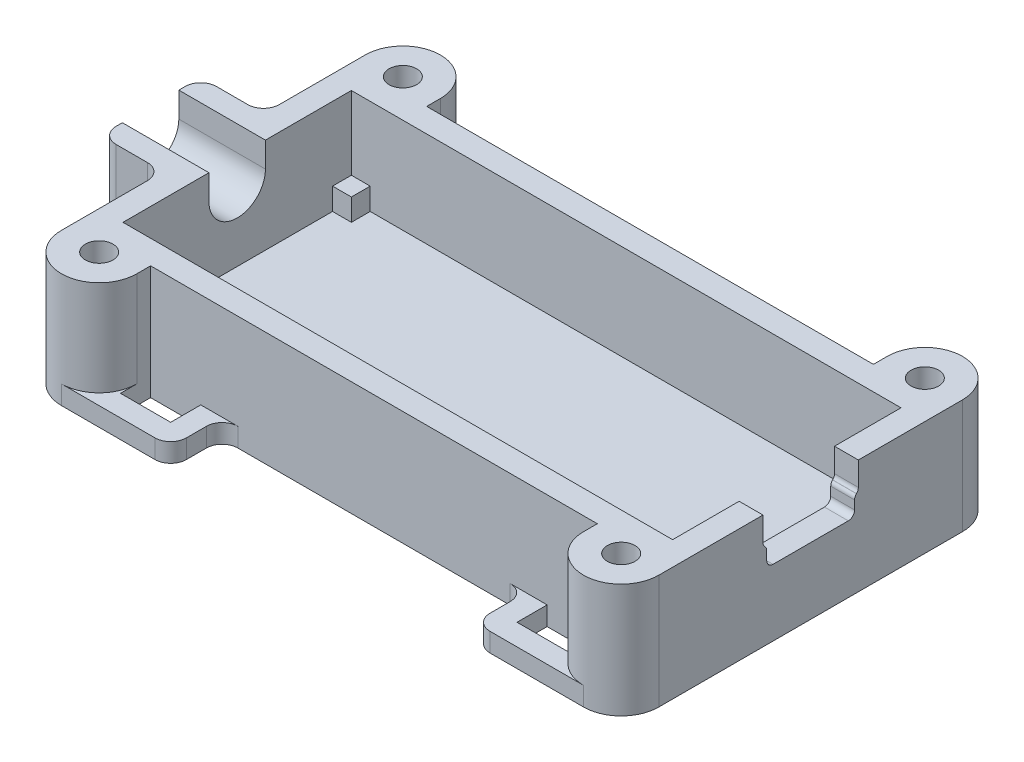
SolidWorks part; units mm, degrees
ref_plane "Front Plane" through (0, 0, 0) normal (0, 0, 1) x (1, 0, 0)
ref_plane "Top Plane" through (0, 0, 0) normal (0, 1, 0) x (1, 0, 0)
ref_plane "Right Plane" through (0, 0, 0) normal (1, 0, 0) x (0, 0, -1)
sketch "Sketch1" plane through (0, 0, 0) normal (0, 1, 0) x (1, 0, 0)
  line L0 (-21.9, 9.1) -> (-23.8, 9.1) construction
  line L1 (-21.9, 9.1) -> (21.9, 9.1)
  line L2 (-21.9, 9.1) -> (-21.9, -9.1)
  line L3 (-21.9, -9.1) -> (21.9, -9.1)
  line L4 (21.9, 9.1) -> (21.9, -9.1)
  line L5 (-21.9, 9.1) -> (21.9, -9.1) construction
  line L6 (-21.9, -9.1) -> (21.9, 9.1) construction
  line L7 (23.8, -11) -> (-23.8, -11)
  line L8 (23.8, -11) -> (23.8, 11)
  line L9 (23.8, 11) -> (-23.8, 11)
  line L10 (-23.8, -11) -> (-23.8, 11)
  line L11 (23.8, -11) -> (-23.8, 11) construction
  line L12 (23.8, 11) -> (-23.8, -11) construction
  line L13 (-21.9, 9.1) -> (-21.9, 11) construction
  line L14 (-19.7, 12.1) -> (-17.8, 12.1) construction
  line L15 (-23.8, 12.1) -> (-23.8, 11)
  line L16 (0, 30.5142) -> (0, -27.0472) construction
  line L17 (-40.1948, 0) -> (31.8876, 0) construction
  line L18 (-17.8, 12.1) -> (-17.8, 11)
  line L19 (17.8, 12.1) -> (17.8, 11)
  line L20 (23.8, 12.1) -> (23.8, 11)
  line L21 (23.8, -12.1) -> (23.8, -11)
  line L22 (17.8, -12.1) -> (17.8, -11)
  line L23 (-17.8, -12.1) -> (-17.8, -11)
  line L24 (-23.8, -12.1) -> (-23.8, -11)
  line L26 (-28.8, 4) -> (-23.8, 4)
  line L27 (-28.8, 4) -> (-28.8, -4)
  line L28 (-28.8, -4) -> (-23.8, -4)
  line L29 (-23.8, 4) -> (-23.8, -4)
  line L30 (-28.8, 4) -> (-23.8, -4) construction
  line L31 (-28.8, -4) -> (-23.8, 4) construction
  circle A0 centre (-20.8, 12.1) radius 1.1
  circle A1 centre (-20.8, 12.1) radius 3
  circle A2 centre (20.8, 12.1) radius 1.1
  circle A3 centre (20.8, 12.1) radius 3
  circle A4 centre (20.8, -12.1) radius 1.1
  circle A5 centre (20.8, -12.1) radius 3
  circle A6 centre (-20.8, -12.1) radius 1.1
  circle A7 centre (-20.8, -12.1) radius 3
  point P0 (0, 0)
  point P6 (0, 0)
  point P42 (-26.3, 0)
  dimension "D4" = 2.2
  dimension "D5" = 5
  dimension "D3" = 6
  dimension "D1" = 18.2
  dimension "D2" = 43.8
  dimension "D6" = 8
extrude "Boss-Extrude1" add sketch "Sketch1" along normal blind 7.6 contours A1 L9 L18 | L9 A1 A0 | A1 L15 L9 | L9 A3 L19 | A3 L9 A2 | L20 A3 L9 | A5 L7 L22 | A5 L7 A4 | A5 L21 L7 | L24 A7 L7 | A7 L7 A6 | L7 A7 L23 | L7 A7 L3 L2 L1 A1 L9 L10 | A7 L7 | L3 A7 L7 A5 | L7 A5 | A5 L7 L8 L9 A3 L1 L4 L3 | A3 L9 | L1 A3 L9 A1 | A1 L9 | L27 L28 L10 L26
sketch "Sketch3" plane through (0, 0, 0) normal (0, -1, 0) x (1, 0, 0)
  line L8 (-23.8, -4) -> (-23.8, -12.1)
  line L9 (-17.8, -12.1) -> (-17.8, -11)
  line L10 (-17.8, -11) -> (17.8, -11)
  line L11 (17.8, -11) -> (17.8, -12.1)
  line L12 (23.8, -12.1) -> (23.8, 12.1)
  line L13 (17.8, 12.1) -> (17.8, 11)
  line L14 (17.8, 11) -> (-17.8, 11)
  line L15 (-17.8, 11) -> (-17.8, 12.1)
  line L16 (-23.8, -4) -> (-23.8, -12.1)
  line L17 (-17.8, -12.1) -> (-17.8, -11)
  line L18 (-17.8, -11) -> (17.8, -11)
  line L19 (17.8, -11) -> (17.8, -12.1)
  line L20 (23.8, -12.1) -> (23.8, 12.1)
  line L21 (17.8, 12.1) -> (17.8, 11)
  line L22 (17.8, 11) -> (-17.8, 11)
  line L23 (-17.8, 11) -> (-17.8, 12.1)
  line L28 (-23.8, 12.1) -> (-23.8, 4)
  line L29 (-23.8, 12.1) -> (-23.8, 4)
  line L30 (-23.8, 4) -> (-28.8, 4)
  line L31 (-23.8, 4) -> (-28.8, 4)
  line L32 (-28.8, 4) -> (-28.8, -4)
  line L33 (-28.8, 4) -> (-28.8, -4)
  line L34 (-28.8, -4) -> (-23.8, -4)
  line L35 (-28.8, -4) -> (-23.8, -4)
  circle A0 centre (-20.8, -12.1) radius 1.1 construction
  circle A1 centre (20.8, -12.1) radius 1.1 construction
  circle A2 centre (20.8, 12.1) radius 1.1 construction
  circle A3 centre (-20.8, 12.1) radius 1.1 construction
  arc A4 (-17.8, 12.1) -> (-23.8, 12.1) centre (-20.8, 12.1) ccw
  arc A5 (-23.8, -12.1) -> (-17.8, -12.1) centre (-20.8, -12.1) ccw
  arc A6 (17.8, -12.1) -> (23.8, -12.1) centre (20.8, -12.1) ccw
  arc A7 (23.8, 12.1) -> (17.8, 12.1) centre (20.8, 12.1) ccw
  arc A8 (-17.8, 12.1) -> (-23.8, 12.1) centre (-20.8, 12.1) ccw
  arc A9 (-23.8, -12.1) -> (-17.8, -12.1) centre (-20.8, -12.1) ccw
  arc A10 (17.8, -12.1) -> (23.8, -12.1) centre (20.8, -12.1) ccw
  arc A11 (23.8, 12.1) -> (17.8, 12.1) centre (20.8, 12.1) ccw
  circle A12 centre (-20.8, -12.1) radius 1.1
  circle A13 centre (20.8, -12.1) radius 1.1
  circle A14 centre (20.8, 12.1) radius 1.1
  circle A15 centre (-20.8, 12.1) radius 1.1
  dimension "D1" = 0
extrude "Boss-Extrude2" add sketch "Sketch3" along normal blind 1.5
sketch "Sketch4" plane through (-28.8, 0, 0) normal (-1, 0, 0) x (0, 0, 1)
  line L0 (-9.1, 0) -> (9.1, 0) construction
  line L1 (-9.1, 0) -> (9.1, 0)
  line L2 (0, 7.6) -> (0, -1.5) construction
  line L3 (-4, 7.6) -> (-12.1, 7.6) construction
  line L5 (0, 3.35) -> (12.1, 3.35) construction
  line L6 (12.1, 7.6) -> (12.1, -1.5) construction
  line L7 (-2.25, 5.6) -> (-2.25, 7.6)
  line L8 (2.25, 5.6) -> (2.25, 7.6)
  line L9 (-2.25, 7.6) -> (2.25, 7.6)
  line L11 (-4, 7.6) -> (4, 7.6) construction
  line L12 (4, -1.5) -> (-4, -1.5) construction
  circle A0 centre (0, 5.6) radius 2.25
  dimension "D2" = 4.5
  dimension "D1" = 3.35
extrude "Cut-Extrude1" cut sketch "Sketch4" against normal up to next
sketch "Sketch5" plane through (0, 0, 0) normal (0, 1, 0) x (1, 0, 0)
  line L0 (0, 18.1559) -> (0, -18.574) construction
  line L1 (-21.9, 9.1) -> (-20.4, 9.1)
  line L2 (-21.9, 9.1) -> (-21.9, 7.6)
  line L3 (-21.9, 7.6) -> (-20.4, 7.6)
  line L4 (-20.4, 9.1) -> (-20.4, 7.6)
  line L5 (-28.7323, 0) -> (29.8474, 0) construction
  line L6 (21.9, 9.1) -> (21.9, 7.6)
  line L7 (21.9, 9.1) -> (20.4, 9.1)
  line L8 (20.4, 9.1) -> (20.4, 7.6)
  line L9 (21.9, 7.6) -> (20.4, 7.6)
  line L10 (-21.9, -9.1) -> (-21.9, -7.6)
  line L11 (-21.9, -9.1) -> (-20.4, -9.1)
  line L12 (-20.4, -9.1) -> (-20.4, -7.6)
  line L13 (-21.9, -7.6) -> (-20.4, -7.6)
  line L14 (21.9, -9.1) -> (21.9, -7.6)
  line L15 (21.9, -9.1) -> (20.4, -9.1)
  line L16 (20.4, -9.1) -> (20.4, -7.6)
  line L17 (21.9, -7.6) -> (20.4, -7.6)
  dimension "D1" = 1.5
extrude "Boss-Extrude3" add sketch "Sketch5" along normal blind 1.75
sketch "Sketch6" plane through (23.8, 0, 0) normal (1, 0, 0) x (0, 0, -1)
  line L1 (0, 7.6) -> (0, -1.5) construction
  line L2 (12.1, 7.6) -> (-12.1, 7.6) construction
  line L3 (12.1, -1.5) -> (-12.1, -1.5) construction
  line L4 (7.6, 0) -> (-7.6, 0) construction
  line L5 (7.6, 0) -> (-7.6, 0)
  line L6 (-3.8, 5.2) -> (3.8, 5.2) construction
  line L7 (-3.8, 7.6) -> (3.8, 7.6)
  line L8 (-3.8, 7.6) -> (-3.8, 3.8)
  line L9 (-3.8, 3.8) -> (3.8, 3.8)
  line L10 (3.8, 7.6) -> (3.8, 3.8)
  line L11 (-3.8, 7.6) -> (3.8, 3.8) construction
  line L12 (-3.8, 3.8) -> (3.8, 7.6) construction
  line L13 (-3.5, 5.2) -> (-3.5, 3.8)
  line L14 (-3.5, 5.2) -> (-3.8, 5.5)
  line L15 (3.5, 5.2) -> (3.5, 3.8)
  line L16 (3.5, 5.2) -> (3.8, 5.5)
  point P8 (0, 5.7)
  line M9 (12.1, 7.6) -> (-12.1, 7.6)
  dimension "D1" = 3.8
  dimension "D2" = 7.6
  dimension "D3" = 1.4
  dimension "D4" = 7
  dimension "D5" = 45
extrude "Cut-Extrude2" cut sketch "Sketch6" against normal up to next contours L10 L8 L9 M9
sketch "Sketch8" plane through (0, -1.5, 0) normal (0, -1, 0) x (1, 0, 0)
  line L0 (-20.8, 15.1) -> (-12.1, 15.1)
  line L1 (-17.8, 11) -> (-13.8, 11)
  line L2 (-17.8, 11) -> (-17.8, 13.4)
  line L3 (-17.8, 13.4) -> (-13.8, 13.4)
  line L4 (-13.8, 11) -> (-13.8, 13.4)
  line L5 (-12.1, 15.1) -> (-12.1, 11)
  line L6 (17.8, 11) -> (-17.8, 11) construction
  line L7 (-13.8, 13.4) -> (-13.8, 15.1) construction
  line L8 (-13.8, 13.4) -> (-12.1, 13.4) construction
  line L9 (0, 29.3193) -> (0, -24.0926) construction
  line L10 (-37.5157, 0) -> (37.6606, 0) construction
  line L11 (17.8, 11) -> (13.8, 11)
  line L12 (17.8, 11) -> (17.8, 13.4)
  line L13 (17.8, 13.4) -> (13.8, 13.4)
  line L14 (13.8, 11) -> (13.8, 13.4)
  line L15 (12.1, 15.1) -> (12.1, 11)
  line L16 (20.8, 15.1) -> (12.1, 15.1)
  line L17 (-12.1, -15.1) -> (-12.1, -11)
  line L18 (-20.8, -15.1) -> (-12.1, -15.1)
  line L19 (-17.8, -11) -> (-13.8, -11)
  line L20 (-17.8, -11) -> (-17.8, -13.4)
  line L21 (-17.8, -13.4) -> (-13.8, -13.4)
  line L22 (-13.8, -11) -> (-13.8, -13.4)
  line L23 (20.8, -15.1) -> (12.1, -15.1)
  line L24 (12.1, -15.1) -> (12.1, -11)
  line L25 (13.8, -11) -> (13.8, -13.4)
  line L26 (17.8, -13.4) -> (13.8, -13.4)
  line L27 (17.8, -11) -> (17.8, -13.4)
  line L28 (17.8, -11) -> (13.8, -11)
  arc A0 (-17.8, 12.1) -> (-23.8, 12.1) centre (-20.8, 12.1) ccw construction
  arc M20 (-23.8, -12.1) -> (-17.8, -12.1) centre (-20.8, -12.1) ccw
  line M22 (-17.8, -11) -> (17.8, -11)
  arc M24 (17.8, -12.1) -> (23.8, -12.1) centre (20.8, -12.1) ccw
  arc M26 (23.8, 12.1) -> (17.8, 12.1) centre (20.8, 12.1) ccw
  line M28 (17.8, 11) -> (-17.8, 11)
  arc M30 (-17.8, 12.1) -> (-23.8, 12.1) centre (-20.8, 12.1) ccw
  dimension "D1" = 2.4
  dimension "D2" = 4
extrude "Boss-Extrude4" add sketch "Sketch8" against normal blind 1.5 contours L5 L0 L2 L3 L4 M30 M28 | L16 L15 L14 L13 L12 M26 M28 | L27 L26 L25 L24 L23 M24 M22 | L22 L21 L20 L18 L17 M22 M20
fillet "Fillet1" radius 1.25 12 edges at (-28.8, 3.05, 4) (-28.8, 3.05, -4) (-23.8, 3.05, -4) (-23.8, 3.05, 4) (-12.1, -0.75, -11) (-12.1, -0.75, -15.1) (12.1, -0.75, -15.1) (12.1, -0.75, -11) (12.1, -0.75, 15.1) (12.1, -0.75, 11) (-12.1, -0.75, 11) (-12.1, -0.75, 15.1)
fillet "Fillet2" radius 0.5 6 edges at (22.85, 3.8, 3.5) (22.85, 3.8, -3.5) (22.85, 5.2, -3.5) (22.85, 5.5, -3.8) (22.85, 5.2, 3.5) (22.85, 5.5, 3.8)
